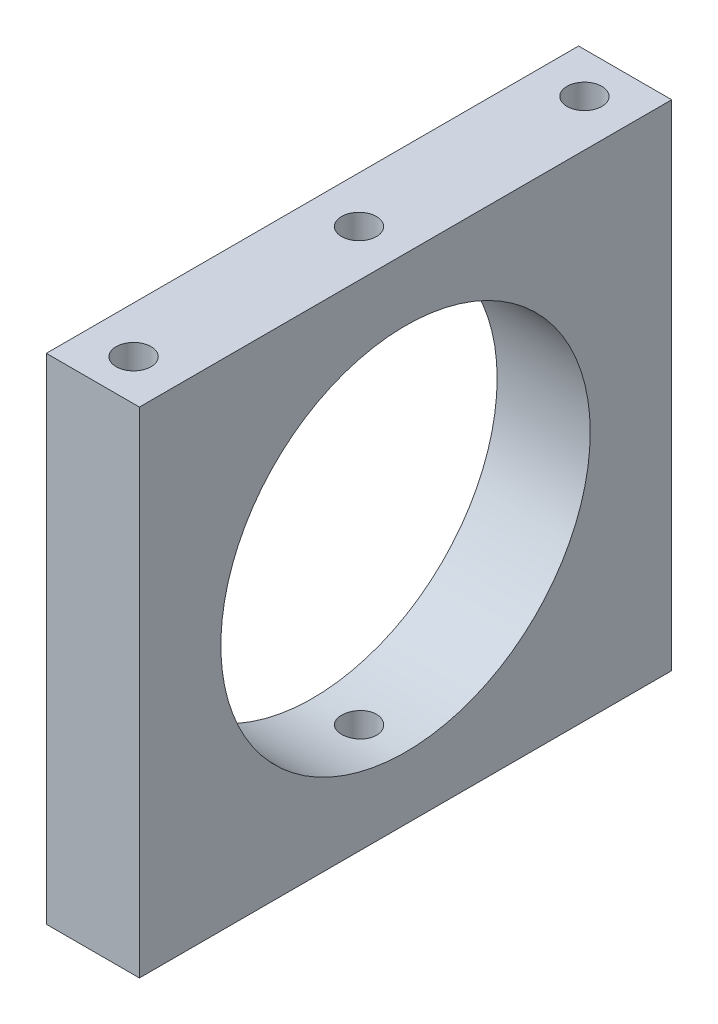
SolidWorks part; units mm, degrees
ref_plane "Front Plane" through (0, 0, 0) normal (0, 0, 1) x (1, 0, 0)
ref_plane "Top Plane" through (0, 0, 0) normal (0, 1, 0) x (1, 0, 0)
ref_plane "Right Plane" through (0, 0, 0) normal (1, 0, 0) x (0, 0, -1)
sketch "Sketch2" plane through (0, 0, 0) normal (0, 1, 0) x (1, 0, 0)
  line L0 (-4.0005, 0) -> (4.0005, 0) construction
  line L1 (-4.0005, -22.875) -> (4.0005, -22.875)
  line L2 (-4.0005, -22.875) -> (-4.0005, 22.875)
  line L3 (-4.0005, 22.875) -> (4.0005, 22.875)
  line L4 (4.0005, -22.875) -> (4.0005, 22.875)
  line L5 (-4.0005, -22.875) -> (4.0005, 22.875) construction
  line L6 (-4.0005, 22.875) -> (4.0005, -22.875) construction
  line L7 (-4.0005, -19.375) -> (4.0005, -19.375) construction
  line L8 (-4.0005, 19.375) -> (4.0005, 19.375) construction
  line L9 (0, 22.875) -> (0, -22.875) construction
  circle A0 centre (0, 0) radius 1.5
  circle A3 centre (0, 19.375) radius 1.5
  circle A4 centre (0, -19.375) radius 1.5
  point P0 (0, 0)
  point P16 (0, -19.38)
  dimension "D3" = 3
  dimension "D6" = 3
  dimension "D7" = 3
  dimension "D4" = 38.75
  dimension "D5" = 19.375
  dimension "D1" = 45.75
  dimension "D2" = 8.001
extrude "Boss-Extrude1" add sketch "Sketch2" along normal blind 42.5
sketch "Sketch3" plane through (4.0005, 0, 0) normal (1, 0, 0) x (0, 0, -1)
  line L0 (0, 42.5) -> (0, 0) construction
  line L1 (-22.875, 42.5) -> (22.875, 42.5) construction
  line L2 (-22.875, 21.25) -> (22.875, 21.25) construction
  line L3 (-22.875, 42.5) -> (-22.875, 0) construction
  line L4 (22.875, 42.5) -> (22.875, 0) construction
  circle A0 centre (0, 21.25) radius 15.875
  dimension "D1" = 31.75
extrude "Cut-Extrude1" cut sketch "Sketch3" against normal blind 42.5
